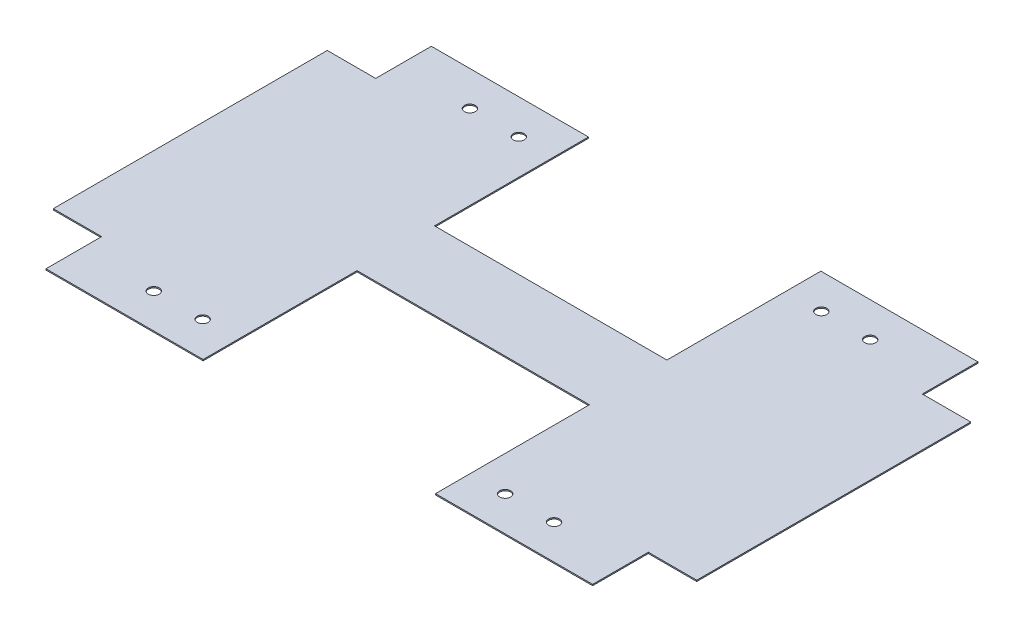
SolidWorks part; units mm, degrees
ref_plane "Front Plane" through (0, 0, 0) normal (0, 0, 1) x (1, 0, 0)
ref_plane "Top Plane" through (0, 0, 0) normal (0, 1, 0) x (1, 0, 0)
ref_plane "Right Plane" through (0, 0, 0) normal (1, 0, 0) x (0, 0, -1)
sketch "Sketch1" plane through (0, 0, 0) normal (0, 1, 0) x (1, 0, 0)
  line L0 (-24, 39.8) -> (-24, 8)
  line L1 (-56.46, 39.8) -> (-24, 39.8)
  line L2 (-66.46, 28.3) -> (-66.46, -28.3)
  line L3 (-56.46, -39.8) -> (-24, -39.8)
  line L4 (66.46, 28.3) -> (66.46, -28.3)
  line L5 (-66.46, 39.8) -> (66.46, -39.8) construction
  line L6 (-66.46, -39.8) -> (66.46, 39.8) construction
  line L7 (-24, 8) -> (24, 8)
  line L8 (24, 8) -> (24, 39.8)
  line L9 (24, -8) -> (24, -39.8)
  line L10 (-24, -39.8) -> (-24, -8)
  line L11 (-24, -8) -> (24, -8)
  line L12 (0, 8) -> (0, -8) construction
  line L13 (24, 39.8) -> (56.46, 39.8)
  line L14 (24, -39.8) -> (56.46, -39.8)
  line L15 (-66.46, -28.3) -> (-56.46, -28.3)
  line L16 (-56.46, -28.3) -> (-56.46, -39.8)
  line L17 (66.46, -28.3) -> (56.46, -28.3)
  line L18 (56.46, -28.3) -> (56.46, -39.8)
  line L19 (66.46, 28.3) -> (56.46, 28.3)
  line L20 (56.46, 28.3) -> (56.46, 39.8)
  line L21 (-56.46, 39.8) -> (-56.46, 28.3)
  line L22 (-56.46, 28.3) -> (-66.46, 28.3)
  circle A0 centre (-41.34, 32.65) radius 1.125
  circle A1 centre (-31.24, 32.65) radius 1.125
  circle A2 centre (31.24, 32.65) radius 1.125
  circle A3 centre (41.34, 32.65) radius 1.125
  circle A4 centre (41.34, -32.65) radius 1.125
  circle A5 centre (31.24, -32.65) radius 1.125
  circle A6 centre (-31.24, -32.65) radius 1.125
  circle A7 centre (-41.34, -32.65) radius 1.125
  point P0 (0, 0)
  dimension "D9" = 2.25
  dimension "D1" = 132.92
  dimension "D2" = 31.8
  dimension "D3" = 16
  dimension "D4" = 48
  dimension "D5" = 11.5
  dimension "D6" = 11.5
  dimension "D7" = 10
  dimension "D8" = 10
  dimension "D10" = 10.1
  dimension "D11" = 10.1
  dimension "D12" = 7.15
  dimension "D13" = 7.15
  dimension "D14" = 7.24
  dimension "D15" = 7.24
  dimension "D16" = 31.8
extrude "Boss-Extrude1" add sketch "Sketch1" along normal blind 0.25
